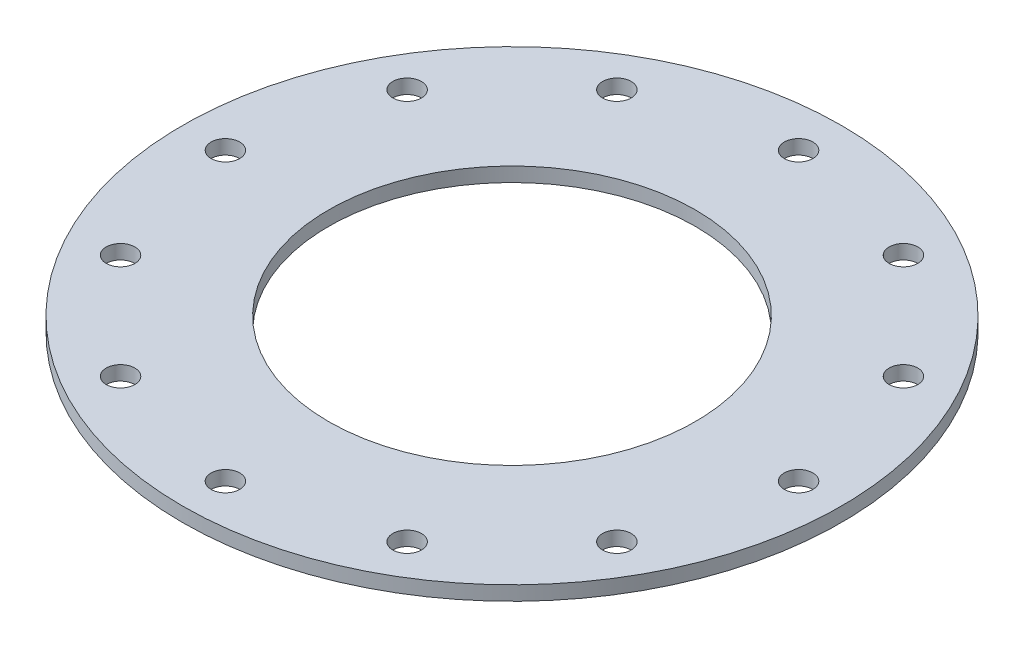
SolidWorks part; units mm, degrees
ref_plane "Front Plane" through (0, 0, 0) normal (0, 0, 1) x (1, 0, 0)
ref_plane "Top Plane" through (0, 0, 0) normal (0, 1, 0) x (1, 0, 0)
ref_plane "Right Plane" through (0, 0, 0) normal (1, 0, 0) x (0, 0, -1)
sketch "Sketch1" plane through (0, 0, 0) normal (0, 1, 0) x (1, 0, 0)
  circle A0 centre (0, 0) radius 73.025
  dimension "D1" = 146.05
extrude "Boss-Extrude1" add sketch "Sketch1" along normal blind 3.175
sketch "Sketch2" plane through (0, 3.175, 0) normal (0, 1, 0) x (1, 0, 0)
  circle A0 centre (63.5, 0) radius 3.175
  circle A1 centre (54.9926, -31.75) radius 3.175
  circle A2 centre (31.75, -54.9926) radius 3.175
  circle A3 centre (0, -63.5) radius 3.175
  circle A4 centre (-31.75, -54.9926) radius 3.175
  circle A5 centre (-54.9926, -31.75) radius 3.175
  circle A6 centre (-63.5, 0) radius 3.175
  circle A7 centre (-54.9926, 31.75) radius 3.175
  circle A8 centre (-31.75, 54.9926) radius 3.175
  circle A9 centre (0, 63.5) radius 3.175
  circle A10 centre (31.75, 54.9926) radius 3.175
  circle A11 centre (54.9926, 31.75) radius 3.175
  point P28 (0, 0)
  dimension "D1" = 6.35
  dimension "D2" = 63.5
  dimension "D3" = 12
extrude "Cut-Extrude1" cut sketch "Sketch2" against normal through all
sketch "Sketch3" plane through (0, 3.175, 0) normal (0, 1, 0) x (1, 0, 0)
  circle A0 centre (0, 0) radius 40.64
extrude "Cut-Extrude2" cut sketch "Sketch3" against normal through all
